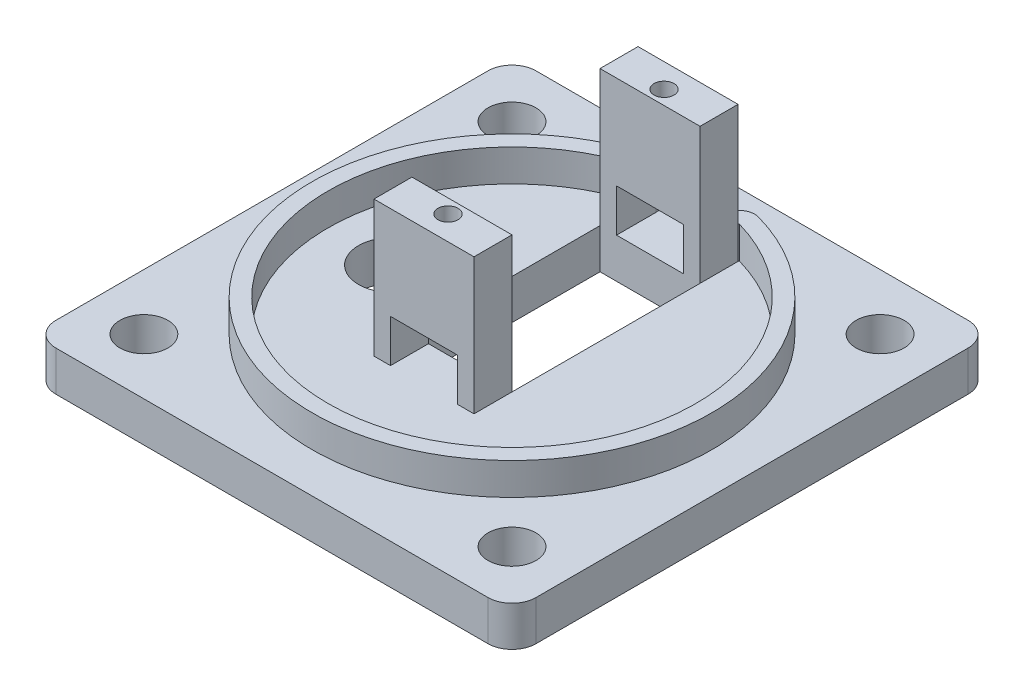
SolidWorks part; units mm, degrees
ref_plane "前视基准面" through (0, 0, 0) normal (0, 0, 1) x (1, 0, 0)
ref_plane "上视基准面" through (0, 0, 0) normal (0, 1, 0) x (1, 0, 0)
ref_plane "右视基准面" through (0, 0, 0) normal (1, 0, 0) x (0, 0, -1)
sketch "草图1" plane through (0, 0, 0) normal (0, 1, 0) x (1, 0, 0)
  line L0 (-30, 30) -> (30, -30) construction
  line L1 (27, 30) -> (-27, 30)
  line L2 (30, 27) -> (30, -27)
  line L3 (27, -30) -> (-27, -30)
  line L4 (-30, 27) -> (-30, -27)
  line L5 (0, -30) -> (0, 30) construction
  line L6 (30, 0) -> (-30, 0) construction
  line L7 (30, 30) -> (-30, -30) construction
  line L9 (6.25, 17.25) -> (-6.25, 17.25)
  line L10 (6.25, 17.25) -> (6.25, -6.25)
  line L11 (6.25, -6.25) -> (-6.25, -6.25)
  line L12 (-6.25, 17.25) -> (-6.25, -6.25)
  line L13 (0, -6.25) -> (0, 17.25) construction
  line L14 (6.25, 5.5) -> (-6.25, 5.5) construction
  circle A0 centre (-23, 23) radius 3
  circle A1 centre (23, 23) radius 3
  circle A2 centre (23, -23) radius 3
  circle A3 centre (-23, -23) radius 3
  arc A4 (-27, -30) -> (-30, -27) centre (-27, -27) cw
  arc A5 (30, -27) -> (27, -30) centre (27, -27) cw
  arc A6 (27, 30) -> (30, 27) centre (27, 27) cw
  arc A7 (-27, 30) -> (-30, 27) centre (-27, 27) ccw
  point P0 (0, 0)
  point P4 (-23, 23)
  point P5 (-23, -23)
  point P6 (23, -23)
  point P7 (23, 23)
  point P28 (0, 5.5)
  dimension "D4" = 6
  dimension "D5" = 3
  dimension "D1" = 60
  dimension "D2" = 60
  dimension "D3" = 7
  dimension "D6" = 12.5
  dimension "D7" = 23.5
  dimension "D8" = 5.5
extrude "凸台-拉伸1" add sketch "草图1" along normal blind 5
sketch "草图2" plane through (0, 5, 0) normal (0, 1, 0) x (1, 0, 0)
  line L0 (-6.25, -6.25) -> (6.25, -6.25) construction
  line L1 (6.25, -6.25) -> (6.25, 17.25) construction
  line L2 (-6.25, 17.25) -> (-6.25, -6.25) construction
  line L3 (6.25, 17.25) -> (-6.25, 17.25) construction
  line L4 (-27, -30) -> (27, -30)
  line L5 (30, -27) -> (30, 27)
  line L6 (27, 30) -> (-27, 30)
  line L7 (-30, 27) -> (-30, -27)
  line L8 (-27, -30) -> (27, -30)
  line L9 (30, -27) -> (30, 27)
  line L10 (27, 30) -> (-27, 30)
  line L11 (-30, 27) -> (-30, -27)
  line L12 (-6.25, -6.25) -> (6.25, -6.25)
  line L13 (6.25, -6.25) -> (6.25, 17.25)
  line L14 (-6.25, 17.25) -> (-6.25, -6.25)
  line L15 (6.25, 17.25) -> (-6.25, 17.25)
  line L16 (-6.25, 5.5) -> (6.25, 5.5) construction
  line L17 (6.25, 17.25) -> (-6.25, 17.25)
  line L18 (6.25, 17.25) -> (6.25, 22)
  line L19 (6.25, 22) -> (-6.25, 22)
  line L20 (-6.25, 17.25) -> (-6.25, 22)
  line L21 (-6.25, -6.25) -> (6.25, -6.25)
  line L22 (-6.25, -6.25) -> (-6.25, -11)
  line L23 (-6.25, -11) -> (6.25, -11)
  line L24 (6.25, -6.25) -> (6.25, -11)
  line L25 (0, 0.4629) -> (0, 10.0331) construction
  circle A0 centre (0, 19) radius 1.25
  circle A1 centre (0, -8) radius 1.25
  arc A4 (-30, -27) -> (-27, -30) centre (-27, -27) ccw
  arc A5 (27, -30) -> (30, -27) centre (27, -27) ccw
  arc A6 (30, 27) -> (27, 30) centre (27, 27) ccw
  arc A7 (-27, 30) -> (-30, 27) centre (-27, 27) ccw
  arc A8 (-30, -27) -> (-27, -30) centre (-27, -27) ccw
  arc A9 (27, -30) -> (30, -27) centre (27, -27) ccw
  arc A10 (30, 27) -> (27, 30) centre (27, 27) ccw
  arc A11 (-27, 30) -> (-30, 27) centre (-27, 27) ccw
  point P20 (-6.25, 5.5)
  point P29 (0, 5.5)
  line M33 (-6.25, 17.25) -> (6.25, 17.25)
  line M35 (6.25, -6.25) -> (-6.25, -6.25)
  dimension "D3" = 2.5
  dimension "D2" = 33
  dimension "D4" = 27
  dimension "D1" = 0
extrude "凸台-拉伸2" add sketch "草图2" along normal blind 17 contours L20 L18 L19 A0 M33 | L24 L22 L23 A1 M35
sketch "草图4" plane through (0, 5, 0) normal (0, 1, 0) x (1, 0, 0)
  line L0 (-6.25, 22) -> (-6.2854, 22.1245)
  line L1 (6.25, 22) -> (6.2854, 22.1245)
  line L4 (-27, -30) -> (27, -30)
  line L5 (30, -27) -> (30, 27)
  line L6 (27, 30) -> (-27, 30)
  line L7 (-30, 27) -> (-30, -27)
  line L8 (-27, -30) -> (27, -30)
  line L9 (30, -27) -> (30, 27)
  line L10 (27, 30) -> (-27, 30)
  line L11 (-30, 27) -> (-30, -27)
  line L16 (6.25, -6.25) -> (6.25, 17.25)
  line L17 (6.25, -11) -> (6.25, -6.25)
  line L18 (-6.25, -11) -> (6.25, -11)
  line L19 (-6.25, -6.25) -> (-6.25, -11)
  line L20 (-6.25, 17.25) -> (-6.25, -6.25)
  line L21 (-6.25, 22) -> (-6.25, 17.25)
  line L22 (6.25, 22) -> (-6.25, 22)
  line L23 (6.25, 17.25) -> (6.25, 22)
  line L24 (6.25, -6.25) -> (6.25, 17.25)
  line L25 (6.25, -11) -> (6.25, -6.25)
  line L26 (-6.25, -11) -> (6.25, -11)
  line L27 (-6.25, -6.25) -> (-6.25, -11)
  line L28 (-6.25, 17.25) -> (-6.25, -6.25)
  line L29 (-6.25, 22) -> (-6.25, 17.25)
  line L30 (6.25, 22) -> (-6.25, 22)
  line L31 (6.25, 17.25) -> (6.25, 22)
  circle A0 centre (0, 0) radius 23
  circle A1 centre (0, 0) radius 25
  arc A6 (-30, -27) -> (-27, -30) centre (-27, -27) ccw
  arc A7 (27, -30) -> (30, -27) centre (27, -27) ccw
  arc A8 (30, 27) -> (27, 30) centre (27, 27) ccw
  arc A9 (-27, 30) -> (-30, 27) centre (-27, 27) ccw
  arc A10 (-30, -27) -> (-27, -30) centre (-27, -27) ccw
  arc A11 (27, -30) -> (30, -27) centre (27, -27) ccw
  arc A12 (30, 27) -> (27, 30) centre (27, 27) ccw
  arc A13 (-27, 30) -> (-30, 27) centre (-27, 27) ccw
  line M19 (-6.25, 22) -> (6.25, 22)
  dimension "D1" = 2
  dimension "D4" = 46
  dimension "D2" = 0
  dimension "D3" = 0
extrude "凸台-拉伸7" add sketch "草图4" along normal blind 4 contours A0 M19 | A1 A0
sketch "草图5" plane through (0, 0, 11) normal (0, 0, 1) x (1, 0, 0)
  line L0 (0, 5) -> (0, 15.7306) construction
  line L2 (4.1857, 10.3348) -> (-4.1857, 10.3348)
  line L3 (4.1857, 10.3348) -> (4.1857, 5)
  line L4 (-6.25, 5) -> (6.25, 5)
  line L5 (6.25, 5) -> (6.25, 22)
  line L6 (6.25, 22) -> (-6.25, 22)
  line L7 (-6.25, 22) -> (-6.25, 5)
  line L9 (6.25, 5) -> (6.25, 22)
  line L10 (6.25, 22) -> (-6.25, 22)
  line L11 (-6.25, 22) -> (-6.25, 5)
  line L12 (4.1857, 5) -> (-4.1857, 5)
  line L13 (-4.1857, 10.3348) -> (-4.1857, 5)
  line L14 (0, 5) -> (0, 10.3348) construction
  line L15 (4.1857, 7.6674) -> (-4.1857, 7.6674) construction
  line L20 (-6.25, 5) -> (6.25, 5)
  point P6 (0, 7.6674)
  dimension "D1" = 0
extrude "切除-拉伸1" cut sketch "草图5" against normal blind 42 contours L2 L13 L20 L3
fillet "圆角1" radius 2 2 edges at (-4.1857, 7, -24.6471) (4.1857, 7, -24.6471)
sketch "草图6" plane through (0, 5, 0) normal (0, 1, 0) x (1, 0, 0)
  circle A0 centre (-14.9619, 0) radius 4.2167
  point P2 (-14.9619, 0)
extrude "切除-拉伸2" cut sketch "草图6" against normal blind 10
